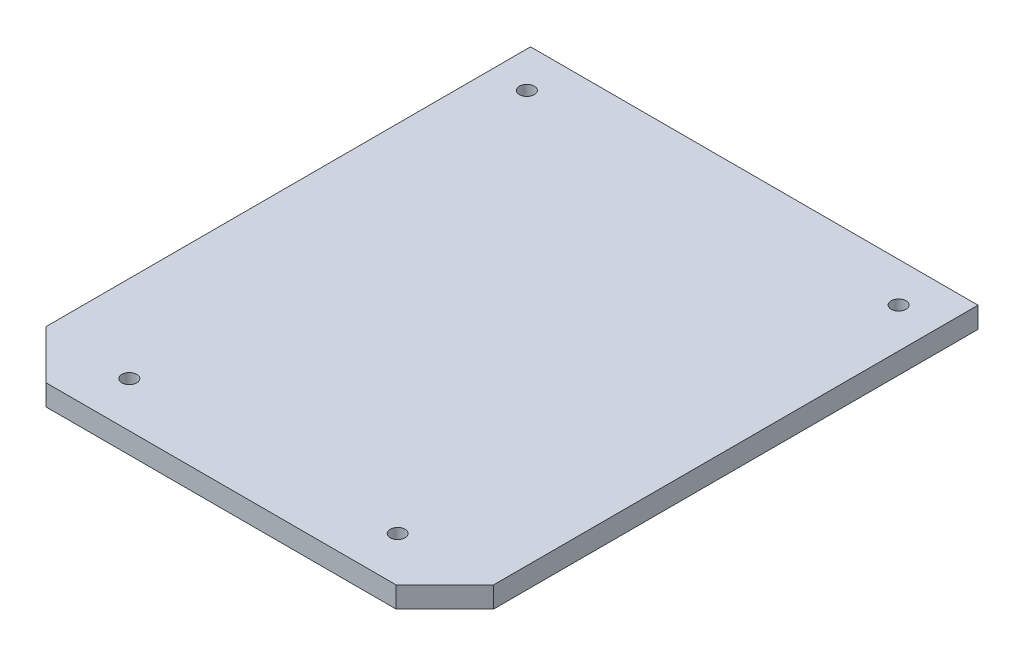
SolidWorks part; units mm, degrees
ref_plane "Front Plane" through (0, 0, 0) normal (0, 0, 1) x (1, 0, 0)
ref_plane "Top Plane" through (0, 0, 0) normal (0, 1, 0) x (1, 0, 0)
ref_plane "Right Plane" through (0, 0, 0) normal (1, 0, 0) x (0, 0, -1)
sketch "Sketch1" plane through (0, 0, 0) normal (0, 1, 0) x (1, 0, 0)
  line L0 (-24.7167, 29.6898) -> (-24.7167, 27.4905)
  line L1 (-24.7167, 6.5966) -> (-22.3996, 4.2795)
  line L2 (-22.3996, 4.2795) -> (-5.7081, 4.2795)
  line L3 (-5.7081, 4.2795) -> (-3.3909, 6.5966)
  line L4 (-3.3909, 6.5966) -> (-3.3909, 29.6898)
  line L5 (-3.3909, 29.6898) -> (-24.7167, 29.6898)
  line L6 (-24.7167, 27.4905) -> (-24.7167, 6.5966)
sketch "Sketch22" plane through (0, 2.0154, 0) normal (0, 1, 0) x (1, 0, 0)
  line L0 (-24.7167, 29.6898) -> (-24.7167, 6.5966)
  line L1 (-24.7167, 6.5966) -> (-22.3996, 4.2795)
  line L2 (-22.3996, 4.2795) -> (-5.7081, 4.2795)
  line L3 (-5.7081, 4.2795) -> (-3.3909, 6.5966)
  line L4 (-3.3909, 6.5966) -> (-3.3909, 29.6898)
  line L5 (-3.3909, 29.6898) -> (-24.7167, 29.6898)
extrude "Boss-Extrude3" add sketch "Sketch22" against normal blind 1
sketch "Sketch23" plane through (0, 2.0154, 0) normal (0, 1, 0) x (1, 0, 0)
  circle A0 centre (-23.0068, 27.8046) radius 0.3538
  circle A1 centre (-5.2891, 27.8046) radius 0.3538
  circle A2 centre (-20.585, 6.4354) radius 0.3538
  circle A3 centre (-7.7952, 6.4354) radius 0.3538
extrude "Cut-Extrude13" cut sketch "Sketch23" against normal blind 4
